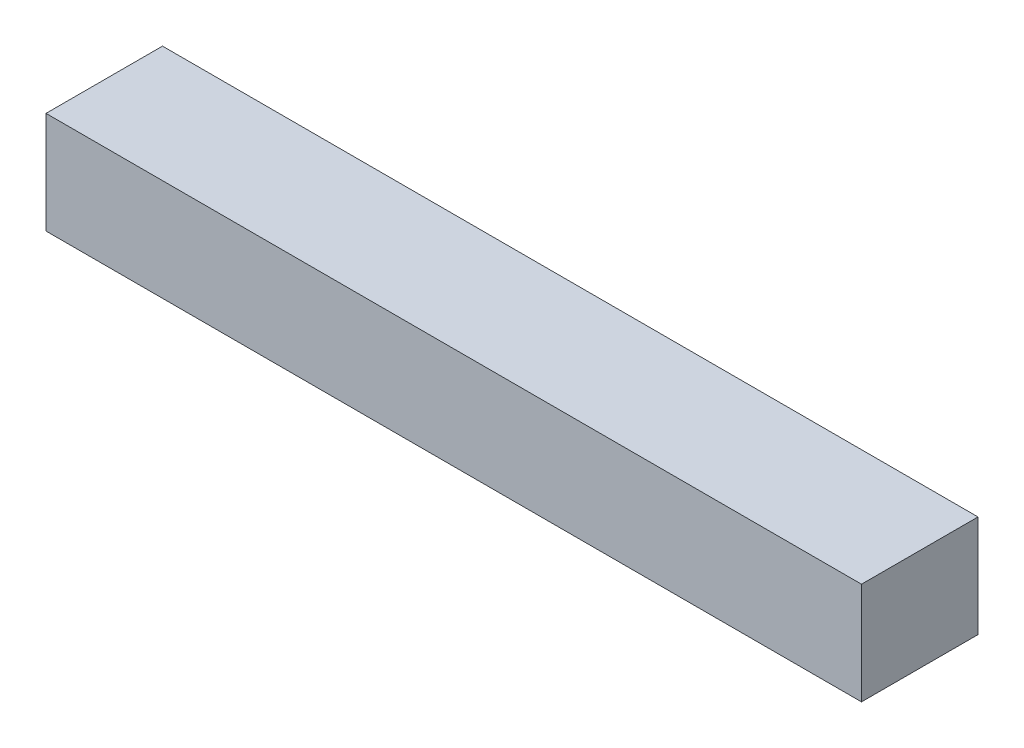
SolidWorks part; units mm, degrees
material "AISI 1020"
ref_plane "Front Plane" through (0, 0, 0) normal (0, 0, 1) x (1, 0, 0)
ref_plane "Top Plane" through (0, 0, 0) normal (0, 1, 0) x (1, 0, 0)
ref_plane "Right Plane" through (0, 0, 0) normal (1, 0, 0) x (0, 0, -1)
sketch "Sketch1" plane through (0, 0, 0) normal (0, 0, 1) x (1, 0, 0)
  line L1 (-28, 3.5) -> (28, 3.5)
  line L2 (-28, 3.5) -> (-28, -3.5)
  line L3 (-28, -3.5) -> (28, -3.5)
  line L4 (28, 3.5) -> (28, -3.5)
  line L5 (-28, 3.5) -> (28, -3.5) construction
  line L6 (-28, -3.5) -> (28, 3.5) construction
  point P0 (0, 0)
  dimension "D1" = 56
  dimension "D2" = 7
extrude "Boss-Extrude1" add sketch "Sketch1" along normal blind 8
scale "Scale1" scale about centroid uniform scaling yes scale factor 2
